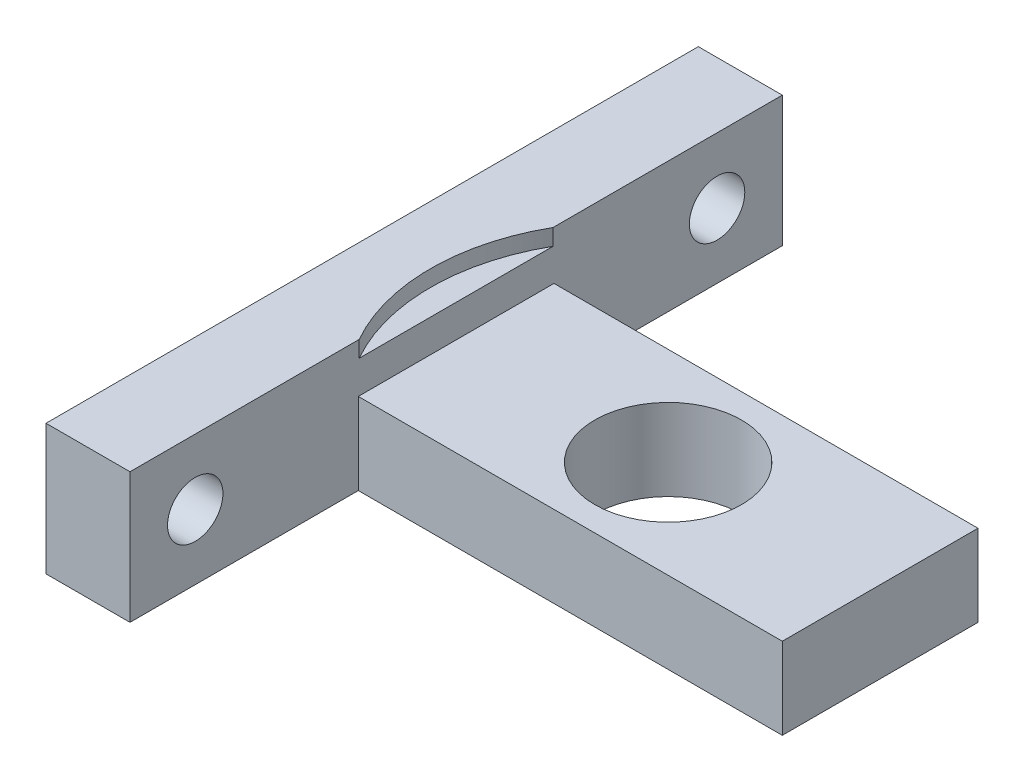
SolidWorks part; units mm, degrees
ref_plane "Alzado" through (0, 0, 0) normal (0, 0, 1) x (1, 0, 0)
ref_plane "Planta" through (0, 0, 0) normal (0, 1, 0) x (1, 0, 0)
ref_plane "Vista lateral" through (0, 0, 0) normal (1, 0, 0) x (0, 0, -1)
sketch "Croquis1" plane through (0, 0, 0) normal (0, 1, 0) x (1, 0, 0)
  line L1 (2.575, -20) -> (-2.575, -20)
  line L2 (2.575, -20) -> (2.575, 20)
  line L3 (2.575, 20) -> (-2.575, 20)
  line L4 (-2.575, -20) -> (-2.575, 20)
  line L5 (2.575, -20) -> (-2.575, 20) construction
  line L6 (2.575, 20) -> (-2.575, -20) construction
  point P0 (0, 0)
  dimension "D1" = 5.15
  dimension "D2" = 40
extrude "Saliente-Extruir1" add sketch "Croquis1" against normal blind 8
sketch "Croquis2" plane through (2.575, 0, 0) normal (1, 0, 0) x (0, 0, -1)
  line L0 (-16, -4) -> (16, -4) construction
  line L1 (-20, 0) -> (20, 0) construction
  circle A0 centre (-16, -4) radius 1.7
  circle A1 centre (16, -4) radius 1.7
  point P4 (0, -4)
  dimension "D1" = 3.4
  dimension "D2" = 32
  dimension "D3" = 4
extrude "Cortar-Extruir1" cut sketch "Croquis2" against normal blind 11
sketch "Croquis3" plane through (0, -8, 0) normal (0, 1, 0) x (1, 0, 0)
  line L0 (2.575, -20) -> (2.575, 20) construction
  line L1 (2.575, 6) -> (28.575, 6)
  line L2 (2.575, 6) -> (2.575, -6)
  line L3 (2.575, -6) -> (28.575, -6)
  line L4 (28.575, 6) -> (28.575, -6)
  line L5 (2.575, 6) -> (28.575, -6) construction
  line L6 (2.575, -6) -> (28.575, 6) construction
  circle A0 centre (15.575, 0) radius 4.5
  point P0 (15.575, 0)
  dimension "D3" = 9
  dimension "D1" = 26
  dimension "D2" = 12
extrude "Saliente-Extruir2" add sketch "Croquis3" along normal blind 5
sketch "Croquis4" plane through (0, 0, 0) normal (0, 1, 0) x (1, 0, 0)
  circle A0 centre (13, 0) radius 12
  dimension "D2" = 24
  dimension "D1" = 13
extrude "Cortar-Extruir2" cut sketch "Croquis4" against normal blind 1
